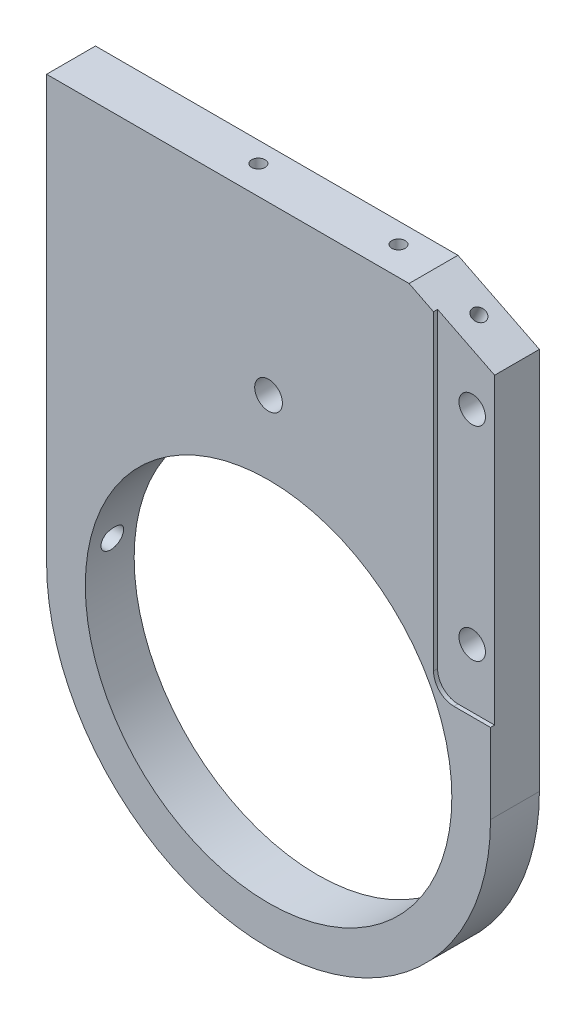
SolidWorks part; units mm, degrees
ref_plane "Alzado" through (0, 0, 0) normal (0, 0, 1) x (1, 0, 0)
ref_plane "Planta" through (0, 0, 0) normal (0, 1, 0) x (1, 0, 0)
ref_plane "Vista lateral" through (0, 0, 0) normal (1, 0, 0) x (0, 0, -1)
sketch "Croquis1" plane through (0, 0, 0) normal (0, 0, 1) x (1, 0, 0)
  line L0 (-54.5, 0) -> (-54.5, 104)
  line L1 (-54.5, 104) -> (34.5, 104)
  line L2 (54.5, 94) -> (54.5, 0)
  line L3 (0, 104.4797) -> (0, 0) construction
  line L4 (34.5, 104) -> (54.5, 94)
  arc A0 (-54.5, 0) -> (54.5, 0) centre (0, 0) ccw
  circle A1 centre (0, 0) radius 45
  dimension "D1" = 54.5
  dimension "D6" = 90
  dimension "D2" = 104
  dimension "D3" = 20
  dimension "D4" = 10
  dimension "D5" = 54.5
extrude "Saliente-Extruir1" add sketch "Croquis1" along normal mid plane 12
hole_wizard "Taladro roscado M41" positions "Croquis3" profile "Croquis2" tap size "M4" standard "DIN"
sketch "Croquis3" plane through (48.5, 97, 0) normal (0.4472, 0.8944, 0) x (-0.8944, 0.4472, 0)
  line L0 (-6.7082, -6) -> (15.6525, -6) construction
  line L1 (-6.7082, 6) -> (-6.7082, -6) construction
  point P0 (4.2918, -1)
  dimension "D1" = 5
  dimension "D2" = 11
sketch "Croquis2" plane through (44.6613, 98.9193, -1) normal (0, 0, 1) x (-0.8944, 0.4472, 0)
  line L0 (0, 0) -> (0, 20.9914)
  line L1 (0, 20.9914) -> (1.65, 20)
  line L2 (1.65, 20) -> (1.65, 0)
  line L5 (1.65, 0) -> (0, 0)
  line L10 (0, 20.9914) -> (-1.65, 20) construction
  line L11 (0, -6.35) -> (0, 107.95) construction
  dimension "Diámetro de perforador para roscar" = 3.3
  dimension "Profundidad de perforador para roscar" = 20
  dimension "Ángulo de perforador" = 118
cosmetic thread "Rosca de taladro1" parameters "D1"=8, "D2"=4
hole_wizard "Taladro roscado M42" positions "Croquis5" profile "Croquis4" tap size "M4" standard "DIN"
sketch "Croquis5" plane through (0, 104, 0) normal (0, 1, 0) x (-1, 0, 0)
  line L0 (-34.5, -6) -> (54.5, -6) construction
  line L1 (54.5, 6) -> (54.5, -6) construction
  point P0 (9.5, -1)
  point P1 (-24.9, -1)
  dimension "D1" = 5
  dimension "D2" = 5
  dimension "D3" = 45
  dimension "D4" = 34.4
sketch "Croquis4" plane through (-9.5, 104, -1) normal (1, 0, 0) x (0, 0, 1)
  line L0 (0, 0) -> (0, 20.9914)
  line L1 (0, 20.9914) -> (1.65, 20)
  line L2 (1.65, 20) -> (1.65, 0)
  line L5 (1.65, 0) -> (0, 0)
  line L10 (0, 20.9914) -> (-1.65, 20) construction
  line L11 (0, -6.35) -> (0, 107.95) construction
  dimension "Diámetro de perforador para roscar" = 3.3
  dimension "Profundidad de perforador para roscar" = 20
  dimension "Ángulo de perforador" = 118
cosmetic thread "Rosca de taladro2" parameters "D1"=8, "D2"=4
cosmetic thread "Rosca de taladro3" parameters "D1"=8, "D2"=4
sketch "Croquis6" plane through (0, 0, 6) normal (0, 0, 1) x (1, 0, 0)
  line L0 (54.5, 0) -> (54.5, 94) construction
  line L1 (40.5, 104) -> (65.6594, 104)
  line L2 (40.5, 104) -> (40.5, 24.6)
  line L3 (45.5, 19.6) -> (65.6594, 19.6)
  line L4 (65.6594, 104) -> (65.6594, 19.6)
  line L5 (34.5, 104) -> (-54.5, 104) construction
  arc A0 (40.5, 24.6) -> (45.5, 19.6) centre (45.5, 24.6) ccw
  dimension "D3" = 5
  dimension "D1" = 14
  dimension "D2" = 84.4
extrude "Cortar-Extruir1" cut sketch "Croquis6" against normal blind 1
sketch "Croquis7" plane through (0, 0, 5) normal (0, 0, 1) x (1, 0, 0)
  line L0 (54.5, 19.6) -> (54.5, 94) construction
  line L1 (34.5, 104) -> (-54.5, 104) construction
  circle A0 centre (49, 84) radius 3.25
  circle A1 centre (49, 34) radius 3.25
  dimension "D4" = 6.5
  dimension "D1" = 5.5
  dimension "D2" = 20
  dimension "D3" = 50
extrude "Cortar-Extruir2" cut sketch "Croquis7" against normal blind 37.7
sketch "Croquis8" plane through (0, 0, -6) normal (0, 0, -1) x (-1, 0, 0)
  circle A0 centre (-49, 84) radius 5
  circle A1 centre (-49, 34) radius 5
  dimension "D1" = 10
extrude "Cortar-Extruir3" cut sketch "Croquis8" against normal blind 6
hole_wizard "Taladro roscado M6x0.51" positions "Croquis11" profile "Croquis10" tap size "M6x0.5" standard "DIN"
sketch "Croquis11" plane through (-54.5, 0, 0) normal (-1, 0, 0) x (0, 0, 1)
  line L0 (6, 104) -> (-6, 104) construction
  point P0 (0, 96.5)
  point P1 (0, 51.7)
  dimension "D1" = 7.5
  dimension "D2" = 44.8
sketch "Croquis10" plane through (-54.5, 96.5, 0) normal (0, 1, 0) x (0, 0, 1)
  line L0 (0, 0) -> (0, 24.1524)
  line L1 (0, 24.1524) -> (2.75, 22.5)
  line L2 (2.75, 22.5) -> (2.75, 0)
  line L5 (2.75, 0) -> (0, 0)
  line L10 (0, 24.1524) -> (-2.75, 22.5) construction
  line L11 (0, -6.35) -> (0, 107.95) construction
  dimension "Diámetro de perforador para roscar" = 5.5
  dimension "Profundidad de perforador para roscar" = 22.5
  dimension "Ángulo de perforador" = 118
cosmetic thread "Rosca de taladro4" parameters "D1"=12, "D2"=6
cosmetic thread "Rosca de taladro5" parameters "D1"=12, "D2"=6
hole_wizard "Taladro roscado M6x0.52" positions "Croquis13" profile "Croquis12" tap size "M6x0.5" standard "DIN"
sketch "Croquis13" plane through (-54.5, 0, 0) normal (-1, 0, 0) x (0, 0, 1)
  point P0 (0, 7.5)
  dimension "D1" = 44.2
sketch "Croquis12" plane through (-54.5, 7.5, 0) normal (0, 1, 0) x (0, 0, 1)
  line L0 (0, 0) -> (0, 12.1524)
  line L1 (0, 12.1524) -> (2.75, 10.5)
  line L2 (2.75, 10.5) -> (2.75, 0)
  line L5 (2.75, 0) -> (0, 0)
  line L10 (0, 12.1524) -> (-2.75, 10.5) construction
  line L11 (0, -6.35) -> (0, 107.95) construction
  dimension "Diámetro de perforador para roscar" = 5.5
  dimension "Profundidad de perforador para roscar" = 10.5
  dimension "Ángulo de perforador" = 118
cosmetic thread "Rosca de taladro6" parameters "D1"=10.5, "D2"=6
hole_wizard "Taladro roscado M81" positions "Croquis16" profile "Croquis15" tap size "M8" standard "DIN" end condition through all
sketch "Croquis16" plane through (0, 0, 6) normal (0, 0, 1) x (1, 0, 0)
  line L0 (-54.5, 104) -> (-54.5, 0) construction
  line L1 (34.5, 104) -> (-54.5, 104) construction
  point P0 (0, 63)
  dimension "D1" = 54.5
  dimension "D2" = 41
sketch "Croquis15" plane through (0, 63, 6) normal (1, 0, 0) x (0, -1, 0)
  line L0 (0, 0) -> (0, 12)
  line L1 (0, 12) -> (3.4, 12)
  line L2 (3.4, 12) -> (3.4, 0)
  line L5 (3.4, 0) -> (0, 0)
  line L11 (0, -6.35) -> (0, 107.95) construction
  dimension "Diámetro de perforador para roscar hasta el siguiente" = 6.8
  dimension "Profundidad de perforador para roscar hasta el siguiente" = 12
cosmetic thread "Rosca de taladro7" parameters "D2"=8
